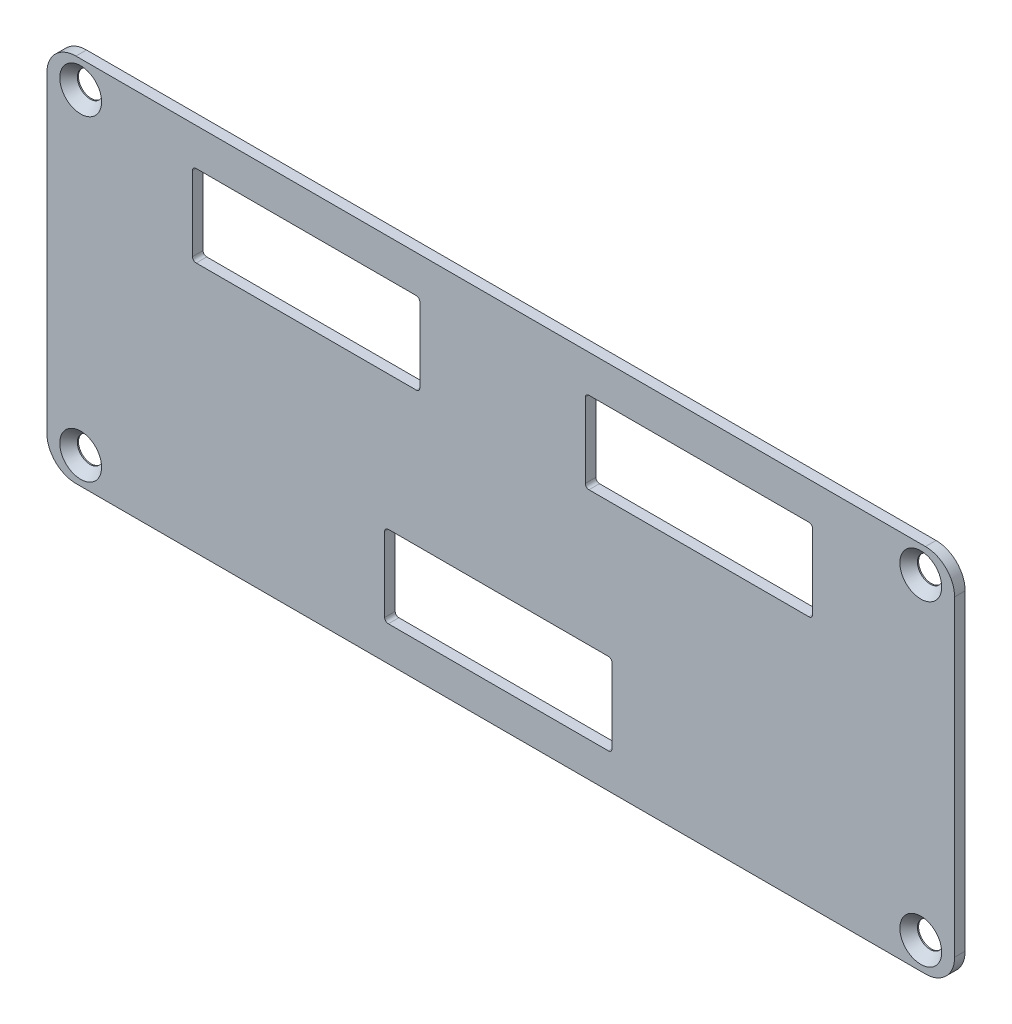
SolidWorks part; units mm, degrees
other "Markup1"
sketch "Sketch3" plane through (0, 0, 0) normal (-0.9973, 0.0561, -0.0476) x (-0.0483, -0.0106, 0.9988)
ref_plane "Front Plane" through (0, 0, 0) normal (0, 0, 1) x (1, 0, 0)
ref_plane "Top Plane" through (0, 0, 0) normal (0, 1, 0) x (1, 0, 0)
ref_plane "Right Plane" through (0, 0, 0) normal (1, 0, 0) x (0, 0, -1)
sketch "Sketch1" plane through (0, 0, 0) normal (0, 0, 1) x (1, 0, 0)
  line L1 (0, 0) -> (124.8, 0)
  line L2 (0, 0) -> (0, -50.9)
  line L3 (0, -50.9) -> (124.8, -50.9)
  line L4 (124.8, 0) -> (124.8, -50.9)
  dimension "D1" = 124.8
  dimension "D2" = 50.9
extrude "Boss-Extrude1" add sketch "Sketch1" along normal blind 1.45
hole_wizard "CSK for M3.5 Flat Head Machine Screw1" positions "3DSketch1" profile "Sketch2" countersink size "M3.5" standard "ANSI Metric" end condition through all
sketch3d "3DSketch1"
  line L0 (124.8, 0, 1.45) -> (0, 0, 1.45) construction
  line L2 (124.8, -50.9, 1.45) -> (124.8, 0, 1.45) construction
  point P0 (4.65, -3.7, 1.45)
  point P2 (120.15, -3.7, 1.45)
  point P4 (120.15, -47.2, 1.45)
  point P6 (4.65, -47.2, 1.45)
  dimension "D3" = 3.7
  dimension "D1" = 115.5
  dimension "D2" = 43.5
  dimension "D4" = 4.65
sketch "Sketch2" plane through (4.65, -3.7, 1.45) normal (1, 0, 0) x (0, -1, 0)
  line L0 (0, 0) -> (0, 1.45)
  line L1 (0, 1.45) -> (1.75, 1.45)
  line L2 (1.75, 1.45) -> (1.75, 1.2942)
  line L3 (1.75, 1.2942) -> (2.875, 0)
  line L5 (2.875, 0) -> (0, 0)
  line L6 (-1.75, 1.2942) -> (-2.875, 0) construction
  line L11 (0, -6.35) -> (0, 107.95) construction
  dimension "Thru Hole Dia." = 3.5
  dimension "Thru Hole Depth" = 1.45
  dimension "Near C'Sink Dia." = 5.75
  dimension "Near C'Sink Angle" = 82
fillet "Fillet2" radius 4 4 edges at (0, 0, 0.725) (124.8, 0, 0.725) (124.8, -50.9, 0.725) (0, -50.9, 0.725)
sketch "Sketch4" plane through (0, 0, 0) normal (0, 0, 1) x (1, 0, 0)
  line L1 (20.026, -5.125) -> (51.276, -5.125)
  line L2 (20.026, -5.125) -> (20.026, -16.375)
  line L3 (20.026, -16.375) -> (51.276, -16.375)
  line L4 (51.276, -5.125) -> (51.276, -16.375)
  line L5 (74.026, -5.125) -> (105.276, -5.125)
  line L6 (74.026, -5.125) -> (74.026, -16.375)
  line L7 (74.026, -16.375) -> (105.276, -16.375)
  line L8 (105.276, -5.125) -> (105.276, -16.375)
  line L9 (46.444, -34.875) -> (77.694, -34.875)
  line L10 (46.444, -34.875) -> (46.444, -46.125)
  line L11 (46.444, -46.125) -> (77.694, -46.125)
  line L12 (77.694, -34.875) -> (77.694, -46.125)
  line L17 (0, 0) -> (124.8, 0)
  line L18 (0, 0) -> (0, -50.9)
  line L19 (0, -50.9) -> (124.8, -50.9)
  line L20 (124.8, 0) -> (124.8, -50.9)
  point P12 (35.651, -5.125)
  point P13 (51.276, -10.75)
  point P14 (35.651, -10.75)
  point P15 (89.651, -10.75)
  point P17 (105.276, -10.75)
  point P18 (89.651, -5.125)
  point P22 (62.069, -40.5)
  point P23 (0, 0)
  point P24 (77.694, -40.5)
  point P25 (62.069, -34.875)
  dimension "D5" = 10.75
  dimension "D6" = 89.651
  dimension "D7" = 40.5
  dimension "D8" = 11.25
  dimension "D1" = 31.25
  dimension "D2" = 50.9
  dimension "D3" = 124.8
  dimension "D4" = 35.651
  dimension "D9" = 62.069
extrude "Cut-Extrude1" cut sketch "Sketch4" along normal up to surface (1.45 mm away) contours L4 L1 L2 L3 | L8 L5 L6 L7 | L12 L9 L10 L11 up to face at (7.525, -3.7, 1.45)
fillet "Fillet3" radius 0.5 12 edges at (77.694, -34.875, 0.725) (77.694, -46.125, 0.725) (46.444, -34.875, 0.725) (46.444, -46.125, 0.725) (74.026, -16.375, 0.725) (74.026, -5.125, 0.725) (105.276, -16.375, 0.725) (105.276, -5.125, 0.725) (51.276, -16.375, 0.725) (51.276, -5.125, 0.725) (20.026, -16.375, 0.725) (20.026, -5.125, 0.725)
equation "\"D3@3DSketch1\"=(50.9-\"D2@3DSketch1\")/2"
equation "\"D4@3DSketch1\"=(124.8-\"D1@3DSketch1\")/2"
